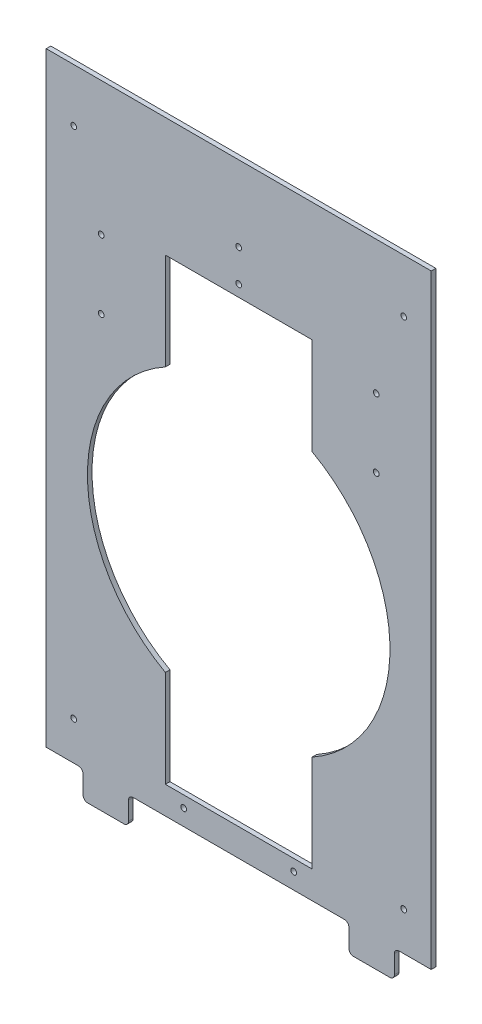
SolidWorks part; units mm, degrees
material "PC High Viscosity"
ref_plane "Front Plane" through (0, 0, 0) normal (0, 0, 1) x (1, 0, 0)
ref_plane "Top Plane" through (0, 0, 0) normal (0, 1, 0) x (1, 0, 0)
ref_plane "Right Plane" through (0, 0, 0) normal (1, 0, 0) x (0, 0, -1)
sketch "Sketch1" plane through (0, 0, 0) normal (0, 0, 1) x (1, 0, 0)
  line L0 (-101.6, 797.56) -> (101.6, 797.56)
  line L1 (-266.7, 0) -> (266.7, 0)
  line L2 (-266.7, 0) -> (-266.7, 2413)
  line L3 (-266.7, 2413) -> (266.7, 2413)
  line L4 (266.7, 0) -> (266.7, 2413)
  line L5 (-101.6, 162.56) -> (101.6, 162.56)
  line L6 (-209.55, 480.06) -> (209.55, 480.06) construction
  line L7 (-101.6, 162.56) -> (-101.6, 296.788)
  line L8 (101.6, 162.56) -> (101.6, 296.788)
  line L9 (101.6, 797.56) -> (101.6, 663.332)
  line L10 (-101.6, 797.56) -> (-101.6, 663.332)
  line L11 (-101.6, 1508.76) -> (-101.6, 1374.532)
  line L12 (-101.6, 873.76) -> (-101.6, 1007.988)
  line L13 (-101.6, 873.76) -> (101.6, 873.76)
  line L14 (101.6, 873.76) -> (101.6, 1007.988)
  line L15 (101.6, 1508.76) -> (101.6, 1374.532)
  line L16 (-101.6, 1508.76) -> (101.6, 1508.76)
  line L17 (-101.6, 2219.96) -> (-101.6, 2085.732)
  line L18 (-101.6, 1584.96) -> (-101.6, 1719.188)
  line L19 (-101.6, 1584.96) -> (101.6, 1584.96)
  line L20 (101.6, 1584.96) -> (101.6, 1719.188)
  line L21 (101.6, 2219.96) -> (101.6, 2085.732)
  line L22 (-101.6, 2219.96) -> (101.6, 2219.96)
  arc A0 (-101.6, 663.332) -> (-101.6, 296.788) centre (0, 480.06) ccw
  arc A1 (101.6, 296.788) -> (101.6, 663.332) centre (0, 480.06) ccw
  arc A2 (-101.6, 1374.532) -> (-101.6, 1007.988) centre (0, 1191.26) ccw
  arc A3 (101.6, 1007.988) -> (101.6, 1374.532) centre (0, 1191.26) ccw
  arc A4 (-101.6, 2085.732) -> (-101.6, 1719.188) centre (0, 1902.46) ccw
  arc A5 (101.6, 1719.188) -> (101.6, 2085.732) centre (0, 1902.46) ccw
  circle A6 centre (0, 480.06) radius 241.3 construction
  point P11 (0, 797.56)
  point P12 (0, 162.56)
  dimension "D3" = 419.1
  dimension "D9" = 482.6
  dimension "D10" = 25.4
  dimension "D1" = 2413
  dimension "D2" = 533.4
  dimension "D4" = 635
  dimension "D5" = 480.06
  dimension "D6" = 203.2
  dimension "D8" = 711.2
  dimension "D11" = 57.15
  dimension "D7" = 3
extrude "Boss-Extrude1" add sketch "Sketch1" along normal blind 6.35
hole_wizard "5/16 (0.3125) Diameter Hole1" positions "Sketch2" profile "Sketch3" hole size "5/16" standard "ANSI Inch" end condition through all
sketch "Sketch2" plane through (0, 0, 6.35) normal (0, 0, 1) x (1, 0, 0)
  line L0 (0, 0) -> (0, 2413) construction
  line L1 (-266.7, 0) -> (266.7, 0) construction
  line L2 (266.7, 2413) -> (-266.7, 2413) construction
  line L4 (-76.2, 146.685) -> (-76.2, 102.235) construction
  line L5 (-76.2, 124.46) -> (0, 124.46) construction
  line L7 (-101.6, 162.56) -> (101.6, 162.56) construction
  line L8 (-266.7, 2413) -> (-266.7, 0) construction
  point P0 (-76.2, 146.685)
  point P4 (-76.2, 102.235)
  point P8 (-228.6, 177.8)
  point P31 (76.2, 102.235)
  point P32 (76.2, 146.685)
  point P43 (-76.2, 857.885)
  point P44 (-76.2, 813.435)
  point P45 (76.2, 813.435)
  point P46 (76.2, 857.885)
  point P47 (-76.2, 1569.085)
  point P48 (-76.2, 1524.635)
  point P49 (76.2, 1524.635)
  point P50 (76.2, 1569.085)
  point P57 (228.6, 177.8)
  point P62 (-228.6, 889)
  point P63 (228.6, 889)
  point P64 (-228.6, 1600.2)
  point P65 (228.6, 1600.2)
  point P68 (0, 2280.285)
  point P70 (0, 2235.835)
  point P72 (228.6, 2311.4)
  point P74 (-228.6, 2311.4)
  dimension "D1" = 44.45
  dimension "D2" = 38.1
  dimension "D3" = 76.2
  dimension "D5" = 711.2
  dimension "D6" = 177.8
  dimension "D7" = 38.1
  dimension "D8" = 711.2
  dimension "D9" = 711.2
  dimension "D10" = 711.2
  dimension "D4" = 3
sketch "Sketch3" plane through (-76.2, 146.685, 6.35) normal (1, 0, 0) x (0, -1, 0)
  line L0 (0, 0) -> (0, 6.35)
  line L1 (0, 6.35) -> (3.9687, 6.35)
  line L2 (3.9687, 6.35) -> (3.9687, 0)
  line L5 (3.9687, 0) -> (0, 0)
  line L11 (0, -6.35) -> (0, 107.95) construction
  dimension "Thru Hole Dia." = 7.9375
  dimension "Thru Hole Depth" = 6.35
sketch "Sketch6" plane through (0, 0, 6.35) normal (0, 0, 1) x (1, 0, 0)
  line L0 (266.7, 0) -> (266.7, 2413) construction
  line L1 (-266.7, 0) -> (266.7, 0)
  line L2 (-266.7, 0) -> (-266.7, 1546.86)
  line L3 (-266.7, 1546.86) -> (266.7, 1546.86)
  line L4 (266.7, 0) -> (266.7, 1546.86)
  line L5 (76.2, 1569.085) -> (76.2, 1524.635) construction
  point P11 (76.2, 1546.86)
extrude "Cut-Extrude1" cut sketch "Sketch6" against normal through all
sketch "Sketch7" plane through (0, 0, 6.35) normal (0, 0, 1) x (1, 0, 0)
  line L0 (266.7, 1546.86) -> (-266.7, 1546.86) construction
  line L1 (-152.654, 1546.86) -> (-215.646, 1546.86)
  line L2 (-152.654, 1546.86) -> (-152.654, 1508.76)
  line L3 (-152.654, 1508.76) -> (-215.646, 1508.76)
  line L4 (-215.646, 1546.86) -> (-215.646, 1508.76)
  line L5 (0, 1584.96) -> (0, 1546.86) construction
  line L6 (-101.6, 1584.96) -> (101.6, 1584.96) construction
  line L7 (152.654, 1546.86) -> (215.646, 1546.86)
  line L8 (215.646, 1546.86) -> (215.646, 1508.76)
  line L9 (152.654, 1508.76) -> (215.646, 1508.76)
  line L10 (152.654, 1546.86) -> (152.654, 1508.76)
  line L11 (-101.6, 1719.188) -> (-101.6, 1584.96) construction
  dimension "D1" = 51.054
  dimension "D2" = 62.992
  dimension "D3" = 38.1
extrude "Boss-Extrude2" add sketch "Sketch7" against normal up to surface (6.35 mm away) contours L2 L1 L4 L3 | L7 L8 L9 L10 up to face at (0, 1979.93, 0)
fillet "Fillet1" radius 6.35 8 edges at (215.646, 1546.86, 3.175) (215.646, 1508.76, 3.175) (152.654, 1508.76, 3.175) (152.654, 1546.86, 3.175) (-152.654, 1546.86, 3.175) (-152.654, 1508.76, 3.175) (-215.646, 1508.76, 3.175) (-215.646, 1546.86, 3.175)
sketch "Sketch8" [suppressed] plane through (0, 0, 6.35) normal (0, 0, 1) x (1, 0, 0)
  line L0 (266.7, 1546.86) -> (266.7, 2413) construction
  line L1 (-266.7, 2413) -> (266.7, 2413)
  line L2 (-266.7, 2413) -> (-266.7, 2336.8)
  line L3 (-266.7, 2336.8) -> (266.7, 2336.8)
  line L4 (266.7, 2413) -> (266.7, 2336.8)
  dimension "D1" = 76.2
extrude "Cut-Extrude2" [suppressed] cut sketch "Sketch8" against normal through all
sketch "Sketch9" plane through (0, 0, 6.35) normal (0, 0, 1) x (1, 0, 0)
  line L0 (266.7, 1546.86) -> (266.7, 2413) construction
  line L1 (-266.7, 2413) -> (266.7, 2413)
  line L2 (-266.7, 2413) -> (-266.7, 2385.06)
  line L3 (-266.7, 2385.06) -> (266.7, 2385.06)
  line L4 (266.7, 2413) -> (266.7, 2385.06)
  dimension "D1" = 27.94
extrude "Cut-Extrude3" cut sketch "Sketch9" against normal through all
hole_wizard "5/16 (0.3125) Diameter Hole2" positions "Sketch11" profile "Sketch12" hole size "5/16" standard "ANSI Inch" end condition through all
sketch "Sketch11" plane through (0, 0, 6.35) normal (0, 0, 1) x (1, 0, 0)
  line L0 (0, 2219.96) -> (0, 1584.96) construction
  line L1 (101.6, 2219.96) -> (-101.6, 2219.96) construction
  line L2 (-101.6, 1584.96) -> (101.6, 1584.96) construction
  point P0 (-190.5, 2200.032)
  point P2 (-190.5, 2104.782)
  point P4 (190.5, 2200.032)
  point P6 (190.5, 2104.782)
  dimension "D1" = 190.5
  dimension "D2" = 19.05
  dimension "D3" = 95.25
sketch "Sketch12" plane through (-190.5, 2200.032, 6.35) normal (1, 0, 0) x (0, -1, 0)
  line L0 (0, 0) -> (0, 6.35)
  line L1 (0, 6.35) -> (3.9687, 6.35)
  line L2 (3.9687, 6.35) -> (3.9687, 0)
  line L5 (3.9687, 0) -> (0, 0)
  line L11 (0, -6.35) -> (0, 107.95) construction
  dimension "Thru Hole Dia." = 7.9375
  dimension "Thru Hole Depth" = 6.35
equation "\"D1@Sketch2\"=1.5+.25"
